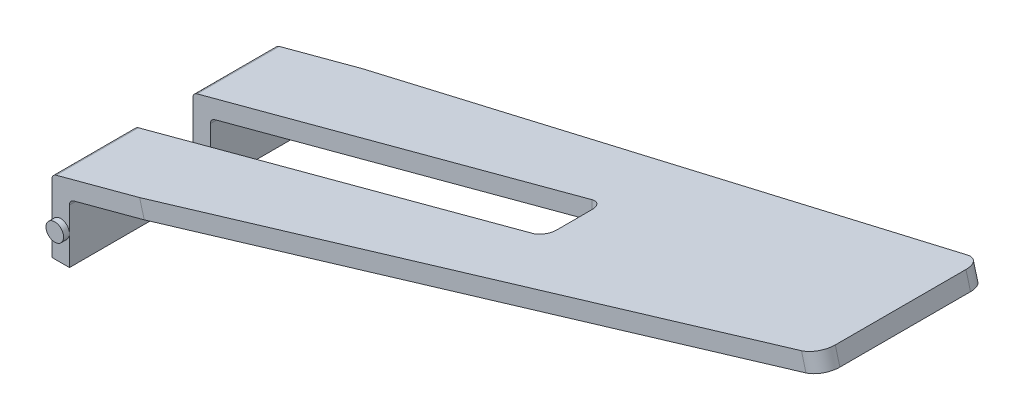
SolidWorks part; units mm, degrees
ref_plane "Front Plane" through (0, 0, 0) normal (0, 0, 1) x (1, 0, 0)
ref_plane "Top Plane" through (0, 0, 0) normal (0, 1, 0) x (1, 0, 0)
ref_plane "Right Plane" through (0, 0, 0) normal (1, 0, 0) x (0, 0, -1)
sketch "Sketch1" plane through (0, 0, 0) normal (0, 0, 1) x (1, 0, 0)
  line L0 (0, 0) -> (0, 1.2302)
  line L1 (0, 1.2302) -> (12.557, 4.5948)
  line L2 (12.557, 4.5948) -> (12.6347, 4.3051)
  line L3 (12.6347, 4.3051) -> (0.3, 1)
  line L4 (0.3, 1) -> (0.3, 0)
  line L5 (0.3, 0) -> (0, 0)
  dimension "D1" = 0.3
  dimension "D2" = 0.3
  dimension "D3" = 1
  dimension "D4" = 105
  dimension "D5" = 13
extrude "Boss-Extrude1" add sketch "Sketch1" along normal blind 3.8
chamfer "Chamfer1" distance 0.5 angle 87.5 2 edges at (12.5959, 4.45, 3.8) (12.5959, 4.45, 0)
sketch "Sketch3" plane through (0, 0, 3.8) normal (0, 0, 1) x (1, 0, 0)
  circle A0 centre (0.15, 0.5) radius 0.15
  dimension "D1" = 0.3
  dimension "D2" = 0.15
  dimension "D3" = 0.5
extrude "Boss-Extrude2" add sketch "Sketch3" along normal blind 0.1 and the other way blind 3.9
sketch "Sketch4" plane through (0, 0, 0) normal (0, -1, 0) x (1, 0, 0)
  line L0 (0, 3.8) -> (0, 0) construction
  line L1 (0, 2.4) -> (7, 2.4)
  line L2 (0, 2.4) -> (0, 1.4)
  line L3 (0, 1.4) -> (7, 1.4)
  line L4 (7, 2.4) -> (7, 1.4)
  line L5 (0, 0) -> (0.3, 0) construction
  point P6 (7, 1.9)
  dimension "D1" = 7
  dimension "D2" = 1
  dimension "D3" = 1.9
extrude "Cut-Extrude2" cut sketch "Sketch4" against normal blind 10
fillet "Fillet1" radius 0.1 4 edges at (0, 1.2302, 0.7) (0, 1.2302, 3.1) (0.3, 1, 0.7) (0.3, 1, 3.1)
fillet "Fillet2" radius 0.3 2 edges at (12.5959, 4.45, 0.5) (12.5959, 4.45, 3.3)
fillet "Fillet3" radius 0.2 2 edges at (7, 2.9506, 2.4) (7, 2.9506, 1.4)
